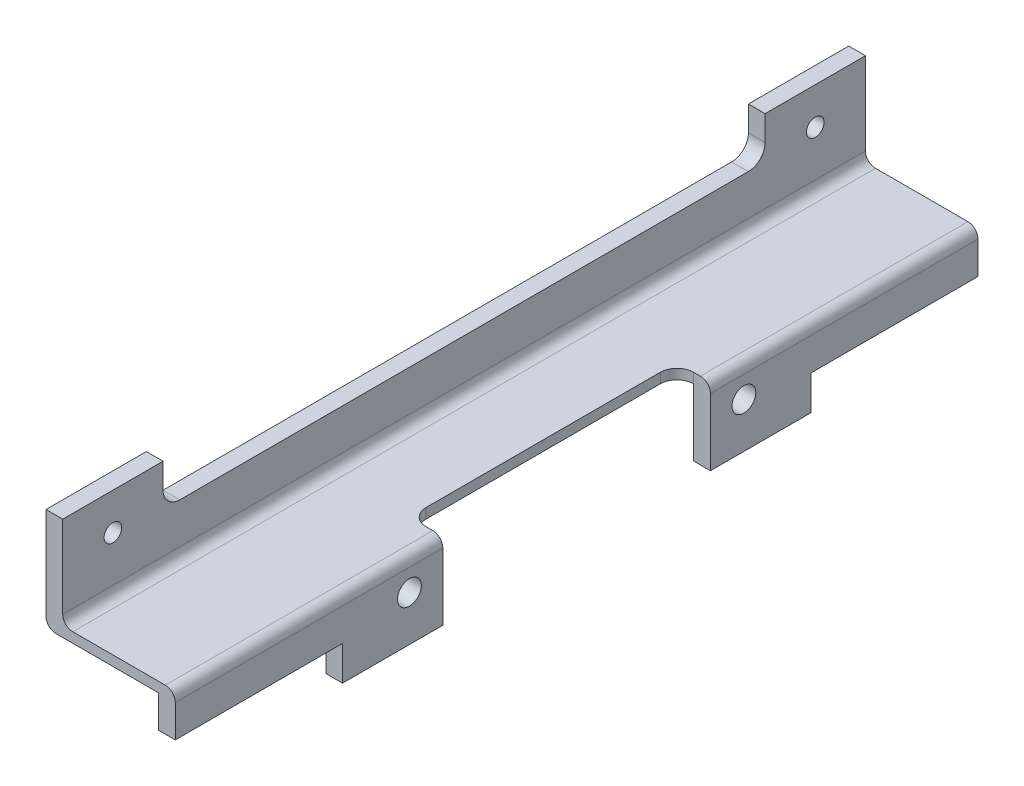
SolidWorks part; units mm, degrees
material "6061-T6 Al"
ref_plane "Front Plane" through (0, 0, 0) normal (0, 0, 1) x (1, 0, 0)
ref_plane "Top Plane" through (0, 0, 0) normal (0, 1, 0) x (1, 0, 0)
ref_plane "Right Plane" through (0, 0, 0) normal (1, 0, 0) x (0, 0, -1)
sketch "Sketch1" plane through (0, 0, 0) normal (0, 0, 1) x (1, 0, 0)
  line L0 (0, 0) -> (50.8, 0)
  line L1 (0, 0) -> (0, 50.8)
  dimension "D1" = 50.8
  dimension "D2" = 50.8
extrude "Extrude-Thin1" add sketch "Sketch1" against normal blind 240 thin thin type one direction wall 6.35
fillet "Fillet1" radius 3 3 edges at (6.35, 6.35, -120) (50.8, 6.35, -120) (6.35, 50.8, -120)
sketch "Sketch3" plane through (0, 6.35, 0) normal (0, 1, 0) x (1, 0, 0)
  line L0 (0, 240) -> (0, 0) construction
  line L1 (32, 245) -> (67, 245)
  line L2 (32, 245) -> (32, -55)
  line L3 (32, -55) -> (67, -55)
  line L4 (67, 245) -> (67, -55)
  line L5 (47.8, 240) -> (9.35, 240) construction
  dimension "D1" = 32
  dimension "D2" = 35
  dimension "D3" = 5
  dimension "D4" = 300
extrude "Extrude2" cut sketch "Sketch3" against normal through all
sketch "Sketch7" plane through (6.35, 0, 0) normal (1, 0, 0) x (0, 0, -1)
  line L0 (240, 0) -> (0, 0) construction
  line L1 (-5, 74) -> (295, 74)
  line L2 (-5, 74) -> (-5, 34)
  line L3 (-5, 34) -> (295, 34)
  line L4 (295, 74) -> (295, 34)
  line L5 (0, 9.35) -> (0, 47.8) construction
  dimension "D1" = 34
  dimension "D2" = 40
  dimension "D3" = 5
  dimension "D4" = 300
extrude "Extrude4" cut sketch "Sketch7" against normal through all
sketch "Sketch10" plane through (6.35, 0, 0) normal (1, 0, 0) x (0, 0, -1)
  line L0 (0, 9.35) -> (0, 34) construction
  line L1 (30, 51.5) -> (210, 51.5)
  line L2 (30, 51.5) -> (30, 26.5)
  line L3 (35, 21.5) -> (205, 21.5)
  line L4 (210, 51.5) -> (210, 26.5)
  line L6 (0, 34) -> (240, 34) construction
  line L7 (240, 0) -> (0, 0) construction
  line L8 (240, 9.35) -> (240, 34) construction
  arc A0 (35, 21.5) -> (30, 26.5) centre (35, 26.5) cw
  arc A1 (210, 26.5) -> (205, 21.5) centre (205, 26.5) cw
  dimension "D6" = 5
  dimension "D1" = 30
  dimension "D2" = 30
  dimension "D3" = 12.5
  dimension "D4" = 30
  dimension "D5" = 21.5
extrude "Extrude5" cut sketch "Sketch10" against normal through all
sketch "Sketch11" plane through (6.35, 0, 0) normal (1, 0, 0) x (0, 0, -1)
  line L0 (0, 9.35) -> (0, 34) construction
  line L1 (240, 9.35) -> (240, 34) construction
  line L2 (0, 34) -> (30, 34) construction
  line L3 (120, 61.8909) -> (120, -15.2982) construction
  line L4 (17.25, 25.25) -> (12.75, 25.25)
  line L5 (12.75, 20.75) -> (17.25, 20.75)
  line L6 (222.75, 25.25) -> (227.25, 25.25)
  line L7 (227.25, 20.75) -> (222.75, 20.75)
  circle A0 centre (225, 23) radius 2.25 construction
  circle A1 centre (15, 23) radius 2.25 construction
  arc A2 (12.75, 25.25) -> (12.75, 20.75) centre (12.75, 23) ccw
  arc A3 (17.25, 20.75) -> (17.25, 25.25) centre (17.25, 23) ccw
  arc A4 (227.25, 25.25) -> (227.25, 20.75) centre (227.25, 23) cw
  arc A5 (222.75, 20.75) -> (222.75, 25.25) centre (222.75, 23) cw
  dimension "D1" = 4.5
  dimension "D7" = 4.5
  dimension "D2" = 15
  dimension "D3" = 15
  dimension "D4" = 11
  dimension "D5" = 2.25
  dimension "D6" = 2.25
hole_wizard "Tapped Hole for #8-32 Helicoil" positions "3DSketch3" profile "Sketch32" tap size "#8-32" standard "Helicoil® Inch" end condition through all
sketch3d "3DSketch3"
  point P0 (6.35, 23, -15)
  point P3 (6.35, 23, -225)
sketch "Sketch32" plane through (6.35, 23, -15) normal (0, 1, 0) x (0, 0, -1)
  line L0 (0, 0) -> (0, 6.35)
  line L1 (0, 6.35) -> (2.1971, 6.35)
  line L3 (2.1971, 6.35) -> (2.1971, 5.08)
  line L4 (2.1971, 5.08) -> (2.6378, 5.08)
  line L5 (2.6378, 5.08) -> (2.6378, 0)
  line L7 (2.6378, 0) -> (0, 0)
  line L11 (0, -6.35) -> (0, 107.95) construction
  dimension "Thru Tap Drill Dia." = 4.3942
  dimension "Thru Tap Drill Depth" = 6.35
  dimension "Thread Major Dia." = 5.2756
  dimension "Thread Depth" = 5.08
sketch "Sketch20" plane through (0, 0, 0) normal (-1, 0, 0) x (0, 0, 1)
  line L0 (-240, 0) -> (-240, 34) construction
  line L1 (-240, 0) -> (0, 0) construction
  line L2 (0, 0) -> (0, 34) construction
  line L3 (-240, 0) -> (-240, 34)
  line L4 (-240, 0) -> (0, 0)
  line L5 (0, 0) -> (0, 34)
  line L6 (0, 34) -> (-240, 34)
extrude "Extrude12" cut sketch "Sketch20" against normal blind 1.35
sketch "Sketch21" plane through (0, 0, 0) normal (0, -1, 0) x (1, 0, 0)
  line L0 (32, -240) -> (1.35, -240) construction
  line L1 (1.35, -240) -> (1.35, 0) construction
  line L2 (32, 0) -> (1.35, 0) construction
  line L3 (32, -240) -> (1.35, -240)
  line L4 (1.35, -240) -> (1.35, 0)
  line L5 (32, 0) -> (1.35, 0)
  line L6 (32, -240) -> (32, 0) construction
  line L7 (32, -240) -> (32, 0)
extrude "Extrude13" cut sketch "Sketch21" against normal blind 3.35
sketch "Sketch22" plane through (32, 0, 0) normal (1, 0, 0) x (0, 0, -1)
  line L0 (240, 3.35) -> (240, 6.35) construction
  line L1 (240, 6.35) -> (0, 6.35) construction
  line L2 (240, 3.35) -> (0, 3.35) construction
  line L3 (0, 3.35) -> (0, 6.35) construction
  line L4 (240, 3.35) -> (240, 6.35)
  line L5 (240, 6.35) -> (0, 6.35)
  line L6 (240, 3.35) -> (0, 3.35)
  line L7 (0, 3.35) -> (0, 6.35)
extrude "Extrude14" add sketch "Sketch22" along normal blind 3
sketch "Sketch23" plane through (0, 0, 0) normal (0, 0, 1) x (1, 0, 0)
  line L0 (35, 6.35) -> (9.35, 6.35) construction
  line L1 (40, 6.35) -> (35, 6.35)
  line L2 (40, 6.35) -> (40, -16.65)
  line L3 (40, -16.65) -> (35, -16.65)
  line L4 (35, 6.35) -> (35, -16.65)
  line L5 (35, 6.35) -> (35, 3.35) construction
  line L6 (35, 3.35) -> (1.35, 3.35) construction
  dimension "D1" = 20
  dimension "D2" = 5
extrude "Extrude15" add sketch "Sketch23" against normal up to surface (240 mm away)
sketch "Sketch24" plane through (40, 0, 0) normal (1, 0, 0) x (0, 0, -1)
  line L0 (0, -16.65) -> (0, 6.35) construction
  line L1 (0, 3.35) -> (240, 3.35) construction
  line L2 (240, -16.65) -> (0, -16.65) construction
  circle A0 centre (170, -3.15) radius 3.5687
  circle A1 centre (70, -3.15) radius 3.5687
  dimension "D1" = 7.1374
  dimension "D2" = 70
  dimension "D3" = 100
  dimension "D4" = 6.5
  dimension "D5" = 13.5
extrude "Extrude16" cut sketch "Sketch24" against normal through all
sketch "Sketch25" plane through (40, 0, 0) normal (1, 0, 0) x (0, 0, -1)
  line L0 (240, -16.65) -> (0, -16.65) construction
  line L1 (80, 34) -> (160, 34)
  line L2 (80, 34) -> (80, -26.65)
  line L3 (80, -26.65) -> (160, -26.65)
  line L4 (160, 34) -> (160, -26.65)
  line L5 (0, 34) -> (30, 34) construction
  circle A0 centre (70, -3.15) radius 3.5687 construction
  circle A2 centre (170, -3.15) radius 3.5687 construction
  circle A3 centre (170, -3.15) radius 3.5687 construction
  dimension "D2" = 10
  dimension "D1" = 10
  dimension "D3" = 10
extrude "Extrude17" cut sketch "Sketch25" against normal blind 10
fillet "Fillet4" radius 5 2 edges at (30, 4.85, -160) (30, 4.85, -80)
sketch "Sketch31" plane through (0, 0, 0) normal (1, 0, 0) x (0, 0, -1)
  line L1 (0, -16.65) -> (50, -16.65)
  line L2 (0, -16.65) -> (0, -6.35)
  line L3 (0, -6.35) -> (50, -6.35)
  line L4 (50, -16.65) -> (50, -6.35)
  line L6 (240, -16.65) -> (190, -16.65)
  line L7 (240, -16.65) -> (240, -6.35)
  line L8 (240, -6.35) -> (190, -6.35)
  line L9 (190, -16.65) -> (190, -6.35)
  line L10 (240, 6.35) -> (0, 6.35) construction
  dimension "D1" = 50
  dimension "D2" = 50
  dimension "D3" = 12.7
  dimension "D4" = 12.7
extrude "Extrude23" cut sketch "Sketch31" along normal through all
fillet "Fillet5" radius 3 3 edges at (40, 6.35, -200) (40, 6.35, -40) (1.35, 3.35, -120)
